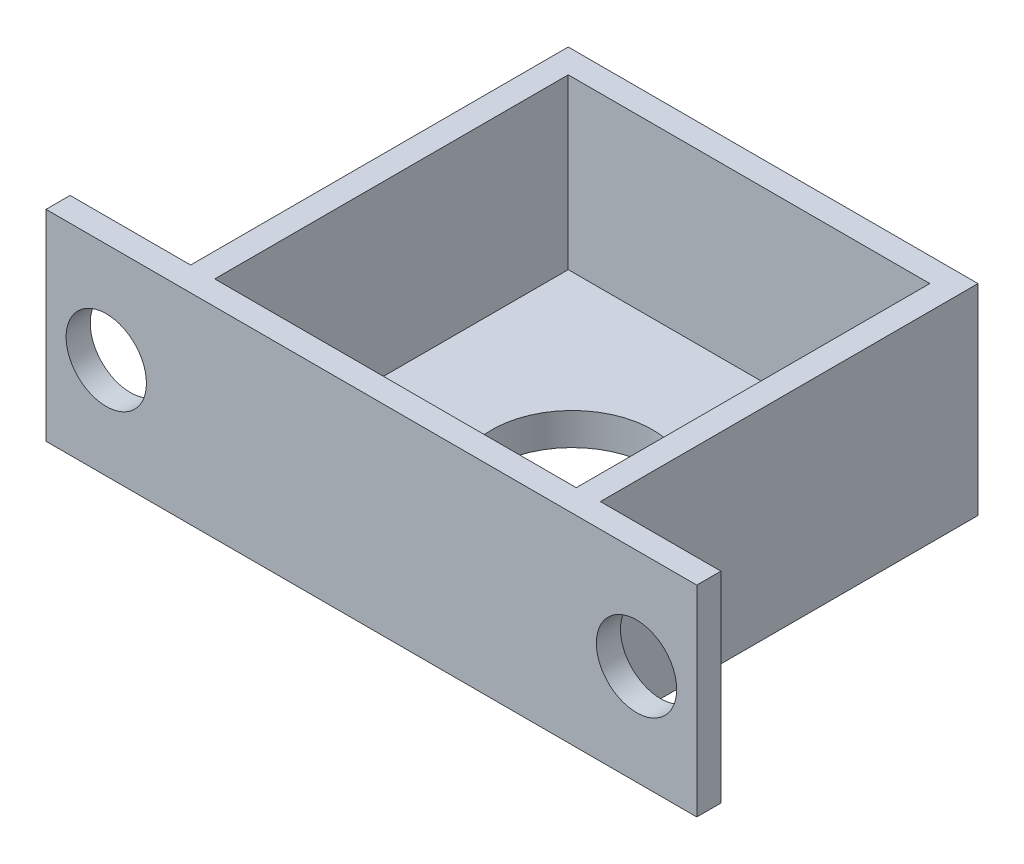
SolidWorks part; units mm, degrees
ref_plane "前基準面" through (0, 0, 0) normal (0, 0, 1) x (1, 0, 0)
ref_plane "上基準面" through (0, 0, 0) normal (0, 1, 0) x (1, 0, 0)
ref_plane "右基準面" through (0, 0, 0) normal (1, 0, 0) x (0, 0, -1)
sketch "草圖1" plane through (0, 0, 0) normal (0, 1, 0) x (1, 0, 0)
  line L1 (-25.5, 25) -> (25.5, 25)
  line L2 (-25.5, 25) -> (-25.5, -25)
  line L3 (-25.5, -25) -> (25.5, -25)
  line L4 (25.5, 25) -> (25.5, -25)
  line L5 (-25.5, 25) -> (25.5, -25) construction
  line L6 (-25.5, -25) -> (25.5, 25) construction
  point P0 (0, 0)
  dimension "D1" = 50
  dimension "D2" = 51
extrude "填料-伸長1" add sketch "草圖1" along normal blind 25
sketch "草圖2" plane through (0, 25, 0) normal (0, 1, 0) x (1, 0, 0)
  circle A0 centre (0, 0) radius 10
  dimension "D1" = 20
extrude "除料-伸長1" cut sketch "草圖2" against normal through all
sketch "草圖3" plane through (0, 25, 0) normal (0, 1, 0) x (1, 0, 0)
  line L1 (-22.5, 22) -> (22.5, 22)
  line L2 (-22.5, 22) -> (-22.5, -22)
  line L3 (-22.5, -22) -> (22.5, -22)
  line L4 (22.5, 22) -> (22.5, -22)
  line L5 (-22.5, 22) -> (22.5, -22) construction
  line L6 (-22.5, -22) -> (22.5, 22) construction
  point P0 (0, 0)
  dimension "D1" = 45
  dimension "D2" = 44
extrude "除料-伸長2" cut sketch "草圖3" against normal blind 21
sketch "草圖4" plane through (0, 0, 22) normal (0, 0, -1) x (-1, 0, 0)
  line L0 (-25.5, 25) -> (-25.5, 0) construction
  line L1 (-40.5, 25) -> (40.5, 25)
  line L2 (-40.5, 25) -> (-40.5, 0)
  line L3 (-40.5, 0) -> (40.5, 0)
  line L4 (40.5, 25) -> (40.5, 0)
  line L5 (25.5, 25) -> (25.5, 0) construction
  line L6 (-25.5, 12.5) -> (-40.5, 12.5) construction
  line L7 (-25.5, 25) -> (-25.5, 0) construction
  line L8 (0, 0) -> (0, 25) construction
  circle A0 centre (-33, 12.5) radius 5
  circle A1 centre (33, 12.5) radius 5
  dimension "D1" = 25
  dimension "D2" = 15
  dimension "D3" = 15
extrude "填料-伸長2" add sketch "草圖4" against normal blind 3
